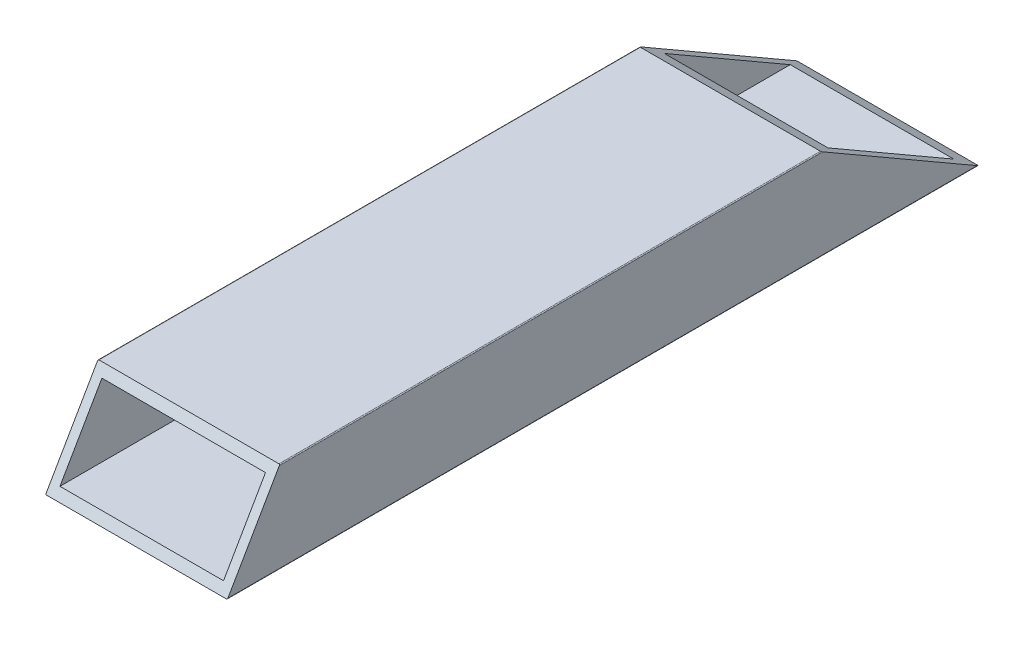
SolidWorks part; units mm, degrees
ref_plane "Front Plane" through (0, 0, 0) normal (0, 0, 1) x (1, 0, 0)
ref_plane "Top Plane" through (0, 0, 0) normal (0, 1, 0) x (1, 0, 0)
ref_plane "Right Plane" through (0, 0, 0) normal (1, 0, 0) x (0, 0, -1)
sketch "Sketch1" plane through (0, 0, 0) normal (0, 0, 1) x (1, 0, 0)
  line L0 (2, 2) -> (38, 2)
  line L1 (0.2, 0) -> (39.8, 0)
  line L2 (0, 0.2) -> (0, 19.8)
  line L3 (0.2, 20) -> (39.8, 20)
  line L4 (40, 0.2) -> (40, 19.8)
  line L5 (38, 2) -> (38, 18)
  line L6 (2, 18) -> (38, 18)
  line L7 (2, 2) -> (2, 18)
  arc A0 (0.2, 0) -> (0, 0.2) centre (0.2, 0.2) cw
  arc A1 (39.8, 0) -> (40, 0.2) centre (39.8, 0.2) ccw
  arc A2 (39.8, 20) -> (40, 19.8) centre (39.8, 19.8) cw
  arc A3 (0, 19.8) -> (0.2, 20) centre (0.2, 19.8) cw
  arc A4 (38, 2) -> (38, 2) centre (38, 2) ccw
  arc A5 (38, 18) -> (38, 18) centre (38, 18) cw
  arc A6 (2, 18) -> (2, 18) centre (2, 18) cw
  arc A7 (2, 2) -> (2, 2) centre (2, 2) cw
  point P7 (0, 0)
  point P10 (40, 0)
  point P13 (40, 20)
  point P16 (0, 20)
  dimension "fillet" = 0.2
  dimension "width" = 40
  dimension "height" = 20
  dimension "thickness" = 2
extrude "Boss-Extrude1" add sketch "Sketch1" along normal blind 165.35
sketch "Sketch2" plane through (0, 0, 0) normal (-1, 0, 0) x (0, 0, 1)
  line L0 (0, 20) -> (34.641, 20)
  line L1 (165.35, 20) -> (0, 20) construction
  line L2 (34.641, 20) -> (0, 0)
  line L3 (0, 0) -> (0, 20)
  line L18 (165.35, 0) -> (153.803, 20)
  line L19 (153.803, 20) -> (165.35, 20)
  line L20 (165.35, 20) -> (165.35, 0)
  dimension "Skew2" = 90
  dimension "Skew1" = 30
extrude "Skew Cut" cut sketch "Sketch2" against normal through all
sketch "Sketch3" plane through (0, 0, 0) normal (-1, 0, 0) x (0, 0, 1)
  line L0 (11.547, 20) -> (0, 0)
  line L2 (153.803, 20) -> (34.641, 20) construction
  line L3 (0, 0) -> (0, 20)
  line L4 (0, 20) -> (11.547, 20)
  dimension "Skew3" = 30
extrude "Cut-Extrude2" [suppressed] cut sketch "Sketch3" against normal through all
sketch "Sketch4" [suppressed] plane through (0, 0, 0) normal (-1, 0, 0) x (0, 0, 1)
  line L0 (259.191, 10.2) -> (160, 10.2) construction
  line L1 (259.191, 3.45) -> (160, 3.45)
  line L2 (259.191, 16.95) -> (160, 16.95)
  line L3 (0, 9.8) -> (0, 0.2) construction
  line L4 (190, 0) -> (0, 0) construction
  line L6 (709.191, 10.2) -> (610, 10.2) construction
  line L8 (709.191, 3.45) -> (610, 3.45)
  line L11 (709.191, 16.95) -> (610, 16.95)
  arc A0 (259.191, 3.45) -> (259.191, 16.95) centre (259.191, 10.2) ccw
  arc A1 (160, 16.95) -> (160, 3.45) centre (160, 10.2) ccw
  arc A4 (709.191, 3.45) -> (709.191, 16.95) centre (709.191, 10.2) ccw
  arc A5 (610, 16.95) -> (610, 3.45) centre (610, 10.2) ccw
  point P2 (209.5955, 10.2)
  point P9 (0, 0)
  point P14 (659.5955, 10.2)
  dimension "D3" = 6.75
  dimension "D4" = 160
  dimension "D1" = 10.2
  dimension "D2" = 99.191
  dimension "D5" = 2
extrude "Cut-Extrude3" [suppressed] cut sketch "Sketch4" against normal blind 10
sketch "Sketch5" plane through (0, 20, 0) normal (0, 1, 0) x (1, 0, 0)
  line L0 (0, -153.9185) -> (0, -34.2946) construction
  line L1 (5.4496, -270.25) -> (15.4496, -270.25)
  line L2 (5.4496, -270.25) -> (5.4496, -331.75)
  line L3 (5.4496, -331.75) -> (15.4496, -331.75)
  line L4 (15.4496, -270.25) -> (15.4496, -331.75)
  line L5 (5.4496, -720.25) -> (15.4496, -720.25)
  line L10 (5.4496, -720.25) -> (5.4496, -781.75)
  line L11 (5.4496, -781.75) -> (15.4496, -781.75)
  line L12 (15.4496, -720.25) -> (15.4496, -781.75)
  point P6 (0, 0)
  dimension "D1" = 5.4496
  dimension "D2" = 10
  dimension "D3" = 61.5
  dimension "D4" = 270.25
  dimension "D5" = 2
extrude "Cut-Extrude4" [suppressed] cut sketch "Sketch5" against normal blind 10
sketch "Sketch6" [suppressed] plane through (20, 0, 0) normal (1, 0, 0) x (0, 0, -1)
  circle A0 centre (-20, 10) radius 2.5
  circle A1 centre (-160, 10) radius 2.5
  dimension "D2" = 140
  dimension "D3" = 5
extrude "Cut-Extrude5" [suppressed] cut sketch "Sketch6" against normal through all
sketch "Sketch7" [suppressed] plane through (0, 10, 0) normal (0, 1, 0) x (1, 0, 0)
  line L0 (0.2, -110) -> (9.8, -110) construction
  line L1 (0.2, -220) -> (0.2, 0) construction
  line L2 (9.8, -220) -> (9.8, 0) construction
  line L3 (9.8, 0) -> (0.2, 0) construction
  circle A0 centre (5, -50) radius 2.15
  circle A1 centre (5, -170) radius 2.15
  point P9 (5, -110)
  point P14 (5, 0)
  dimension "D1" = 4.3
  dimension "D2" = 60
extrude "Cut-Extrude6" [suppressed] cut sketch "Sketch7" against normal through all
sketch "Sketch8" [suppressed] plane through (0, 0, 0) normal (0, -1, 0) x (1, 0, 0)
  line L0 (0.2, 210) -> (9.8, 210) construction
  circle A0 centre (5, 170) radius 2.15
  circle A1 centre (5, 45) radius 2.15
  point P6 (5, 210)
  dimension "D1" = 4.3
  dimension "D2" = 41
  dimension "D3" = 125
extrude "Cut-Extrude7" [suppressed] cut sketch "Sketch8" against normal through all
sketch "Sketch9" [suppressed] plane through (0, 40, 0) normal (0, 1, 0) x (1, 0, 0)
  line L0 (10, -902.5) -> (18, -902.5)
  line L1 (10, -1352.5) -> (18, -1352.5)
  line L2 (10, -1352.5) -> (10, -1422.5)
  line L3 (10, -1422.5) -> (18, -1422.5)
  line L4 (18, -1352.5) -> (18, -1422.5)
  line L5 (10, -902.5) -> (10, -972.5)
  line L6 (10, -972.5) -> (18, -972.5)
  line L7 (18, -902.5) -> (18, -972.5)
  line L8 (39.8, -1572.5) -> (0.2, -1572.5) construction
  line L9 (0, -1572.5) -> (0, 0) construction
  dimension "D2" = 175.25
  dimension "D3" = 10
  dimension "D4" = 5
  dimension "D5" = 61.5
  dimension "D1" = 2
extrude "Cut-Extrude8" [suppressed] cut sketch "Sketch9" against normal blind 10
sketch "Sketch10" [suppressed] plane through (0, 0, 0) normal (-1, 0, 0) x (0, 0, 1)
  line L0 (1374.5, 7.75) -> (1422.5, 7.75) construction
  line L1 (1374.5, 14.5) -> (1422.5, 14.5)
  line L2 (1374.5, 1) -> (1422.5, 1)
  line L3 (1572.5, 39.8) -> (1572.5, 0.2) construction
  line L4 (1572.5, 0) -> (0, 0) construction
  line L5 (924.5, 7.75) -> (972.5, 7.75) construction
  line L6 (924.5, 14.5) -> (972.5, 14.5)
  line L7 (924.5, 1) -> (972.5, 1)
  arc A0 (1374.5, 14.5) -> (1374.5, 1) centre (1374.5, 7.75) ccw
  arc A1 (1422.5, 1) -> (1422.5, 14.5) centre (1422.5, 7.75) ccw
  arc A2 (924.5, 14.5) -> (924.5, 1) centre (924.5, 7.75) ccw
  arc A3 (972.5, 1) -> (972.5, 14.5) centre (972.5, 7.75) ccw
  point P2 (1398.5, 7.75)
  point P14 (948.5, 7.75)
  dimension "D2" = 6.75
  dimension "D1" = 48
  dimension "D3" = 182
  dimension "D4" = 7.75
  dimension "D5" = 2
extrude "Cut-Extrude9" [suppressed] cut sketch "Sketch10" against normal blind 10
sketch "Sketch11" [suppressed] plane through (0, 0, 0) normal (0, -1, 0) x (-1, 0, 0)
  line L0 (-0.2, -1572.5) -> (-39.8, -1572.5) construction
  line L1 (-29, -837.25) -> (-11, -837.25)
  line L2 (-29, -837.25) -> (-29, -735.25)
  line L3 (-29, -735.25) -> (-11, -735.25)
  line L4 (-11, -837.25) -> (-11, -735.25)
  line L5 (-39.8, -1572.5) -> (-39.8, 0) construction
  point P4 (-20, -837.25)
  point P7 (-20, -1572.5)
  point P8 (-29, -786.25)
  point P11 (-39.8, -786.25)
  dimension "D1" = 18
  dimension "D2" = 102
extrude "Cut-Extrude10" [suppressed] cut sketch "Sketch11" against normal blind 10
sketch "Sketch12" [suppressed] plane through (0, 0, 0) normal (0, -1, 0) x (-1, 0, 0)
  line L0 (-40, -786.25) -> (0, -786.25) construction
  line L5 (-0.2, -1572.5) -> (-39.8, -1572.5) construction
  line L7 (0, -1572.5) -> (0, 0) construction
  line L8 (-40, -1572.5) -> (-40, 0) construction
  circle A2 centre (-20, -828.25) radius 2.5
  circle A3 centre (-20, -799.25) radius 5.5
  circle A4 centre (-20, -773.25) radius 5.5
  circle A5 centre (-20, -744.25) radius 2.5
  point P11 (-20, -786.25)
  dimension "D1" = 42
  dimension "D2" = 5
  dimension "D3" = 11
  dimension "D5" = 744.25
  dimension "D4" = 13
extrude "Cut-Extrude11" [suppressed] cut sketch "Sketch12" against normal blind 10
sketch "Sketch13" [suppressed] plane through (0, 0, 0) normal (1, 0, 0) x (0, -1, 0)
  line L0 (0, -400.54) -> (-25.3737, -400.54) construction
  line L1 (-0.2, 0) -> (-39.8, 0) construction
  line L2 (0, -1572.5) -> (0, 0) construction
  line L3 (-39.8, 0) -> (-0.2, 0) construction
  circle A0 centre (-10, -358.54) radius 2.5
  circle A1 centre (-10, -387.54) radius 5.5
  circle A2 centre (-10, -413.54) radius 5.5
  circle A3 centre (-10, -442.54) radius 2.5
  dimension "D2" = 13
  dimension "D3" = 42
  dimension "D4" = 10
  dimension "D5" = 11
  dimension "D6" = 5
  dimension "D1" = 400.54
extrude "Cut-Extrude12" [suppressed] cut sketch "Sketch13" along normal blind 10
